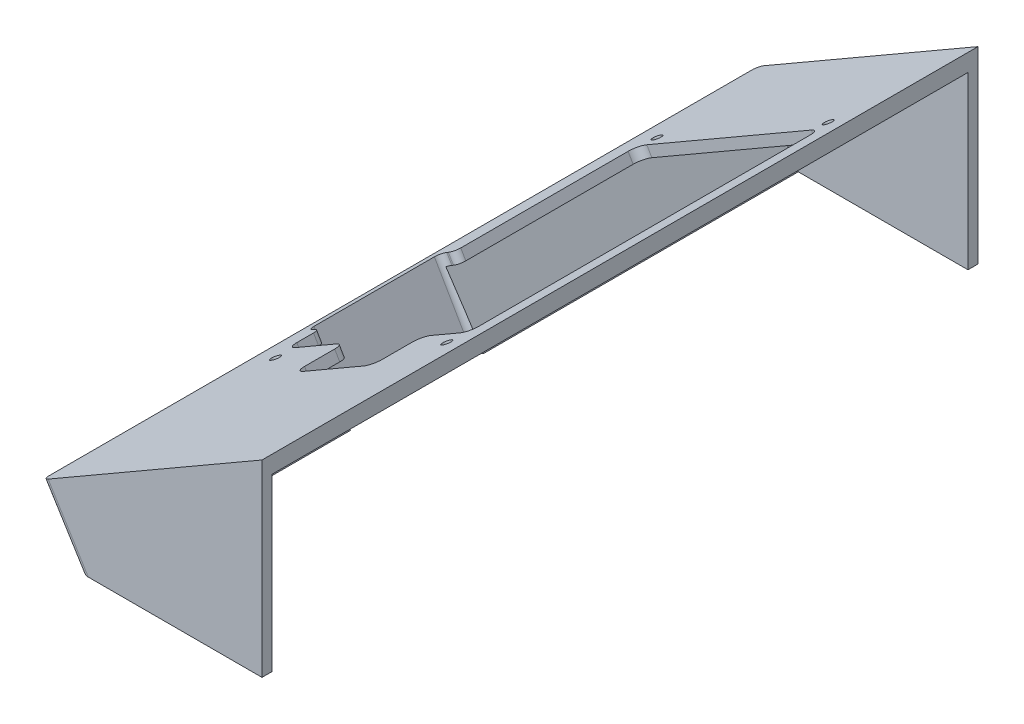
SolidWorks part; units mm, degrees
ref_plane "Front Plane" through (0, 0, 0) normal (0, 0, 1) x (1, 0, 0)
ref_plane "Top Plane" through (0, 0, 0) normal (0, 1, 0) x (1, 0, 0)
ref_plane "Right Plane" through (0, 0, 0) normal (1, 0, 0) x (0, 0, -1)
sketch "Sketch1" plane through (0, 0, 0) normal (0, 0, 1) x (1, 0, 0)
  line L0 (131.5898, 656.4642) -> (185.8342, 656.4642)
  line L3 (185.8342, 656.4642) -> (185.8342, 712.7417)
  line L4 (185.8342, 712.7417) -> (120.1895, 674.8417)
  line L5 (120.1895, 674.8417) -> (131.5898, 656.4642)
extrude "Boss-Extrude1" add sketch "Sketch1" along normal blind 3
sketch "Sketch2" plane through (0, 0, 0) normal (0, 0, 1) x (1, 0, 0)
  line L0 (185.8342, 712.7417) -> (120.1895, 674.8417)
  line L1 (131.5898, 656.4642) -> (135.1202, 656.4642)
  line L2 (120.1895, 674.8417) -> (131.5898, 656.4642)
  line L4 (185.8342, 656.4642) -> (185.8342, 712.7417) construction
  line L7 (131.5898, 656.4642) -> (185.8342, 656.4642) construction
  line L8 (135.1202, 656.4642) -> (124.3711, 673.7919)
  line L9 (185.8342, 656.4642) -> (182.8342, 656.4642)
  line L10 (131.5898, 656.4642) -> (185.8342, 656.4642) construction
  line L11 (185.8342, 656.4642) -> (185.8342, 712.7417) construction
  line L12 (185.8342, 712.7417) -> (120.1895, 674.8417) construction
  line L13 (182.8342, 656.4642) -> (182.8342, 707.5456)
  line L14 (185.8342, 712.7417) -> (120.1895, 674.8417) construction
  line L16 (185.8342, 712.7417) -> (185.8342, 656.4642)
  line L17 (124.3711, 673.7919) -> (182.8342, 707.5456)
  point P0 (135.0746, 656.4642)
  dimension "D2" = 3
  dimension "D3" = 3
  dimension "D4" = 3
extrude "Boss-Extrude2" add sketch "Sketch2" against normal offset from surface (208 mm away) 3
sketch "Sketch10" plane through (0, 0, -208) normal (0, 0, -1) x (-1, 0, 0)
  line L0 (-185.8342, 712.7417) -> (-120.1895, 674.8417)
  line L1 (-120.1895, 674.8417) -> (-131.5898, 656.4642)
  line L2 (-131.5898, 656.4642) -> (-185.8342, 656.4642)
  line L3 (-185.8342, 656.4642) -> (-185.8342, 712.7417)
extrude "Boss-Extrude4" add sketch "Sketch10" along normal blind 3
sketch "Sketch3" plane through (-262.1677, 454.0877, 0) normal (-0.5, 0.866, 0) x (0.866, 0.5, 0)
  line L0 (451.508, 169) -> (508.308, 169)
  line L3 (511.308, 166) -> (511.308, 67)
  line L5 (508.308, 64) -> (498.308, 64)
  line L7 (495.308, 61) -> (495.308, 52)
  line L9 (492.308, 49) -> (471.508, 49)
  line L11 (468.508, 52) -> (468.508, 61)
  line L13 (465.508, 64) -> (451.508, 64)
  line L16 (448.508, 67) -> (448.508, 72)
  line L18 (446.508, 74) -> (446.008, 74)
  line L20 (444.008, 76) -> (444.008, 112)
  line L22 (446.008, 114) -> (446.508, 114)
  line L24 (448.508, 116) -> (448.508, 166)
  line L26 (515.308, 0) -> (515.308, 208) construction
  line L27 (515.308, 208) -> (444.508, 208) construction
  line L28 (441.508, -3) -> (441.508, 211) construction
  arc A5 (448.508, 67) -> (451.508, 64) centre (451.508, 67) ccw
  arc A6 (468.508, 61) -> (465.508, 64) centre (465.508, 61) ccw
  arc A7 (468.508, 52) -> (471.508, 49) centre (471.508, 52) ccw
  arc A8 (492.308, 49) -> (495.308, 52) centre (492.308, 52) ccw
  arc A9 (495.308, 61) -> (498.308, 64) centre (498.308, 61) cw
  arc A10 (508.308, 64) -> (511.308, 67) centre (508.308, 67) ccw
  arc A11 (511.308, 166) -> (508.308, 169) centre (508.308, 166) ccw
  arc A12 (451.508, 169) -> (448.508, 166) centre (451.508, 166) ccw
  arc A13 (446.508, 74) -> (448.508, 72) centre (446.508, 72) cw
  arc A14 (446.008, 74) -> (444.008, 76) centre (446.008, 76) cw
  arc A15 (446.008, 114) -> (444.008, 112) centre (446.008, 112) ccw
  arc A16 (446.508, 114) -> (448.508, 116) centre (446.508, 116) ccw
  circle A17 centre (450.508, 172.9) radius 1.375
  circle A18 centre (509.608, 172.9) radius 1.375
  circle A19 centre (509.608, 58.9) radius 1.375
  circle A20 centre (450.508, 58.9) radius 1.375
  point P0 (0, 0)
  point P8 (446.258, 114)
  point P107 (515.308, 64)
  point P110 (511.308, 169)
  dimension "D1" = 16
  dimension "D11" = 3
  dimension "D12" = 2
  dimension "D2" = 15
  dimension "D3" = 105
  dimension "D4" = 39
  dimension "D5" = 26.8
  dimension "D6" = 20
  dimension "D7" = 10
  dimension "D8" = 4.5
  dimension "D9" = 40
  dimension "D10" = 55
  dimension "D13" = 7
  dimension "D14" = 7
extrude "PiHole" cut sketch "Sketch3" against normal through all both and the other way through all
sketch "Sketch11" plane through (0, 0, 3) normal (0, 0, 1) x (1, 0, 0)
  line L0 (182.8342, 707.5456) -> (185.8342, 707.5456)
  line L1 (185.8342, 656.4642) -> (185.8342, 712.7417) construction
  line L2 (185.8342, 707.5456) -> (185.8342, 656.4642)
  line L3 (185.8342, 656.4642) -> (182.8342, 656.4642)
  line L4 (131.5898, 656.4642) -> (185.8342, 656.4642) construction
  line L5 (182.8342, 656.4642) -> (182.8342, 707.5456)
  point P4 (182.8342, 707.5456)
  dimension "D1" = 3
extrude "Cut-Extrude7" cut sketch "Sketch11" against normal offset from surface (208 mm away) 3 from offset 3 up to face at (155.8619, 675.1279, -211) offset against normal yes
fillet "Fillet1" radius 2 2 edges at (125.8896, 665.6529, 3) (125.8896, 665.6529, -211)
